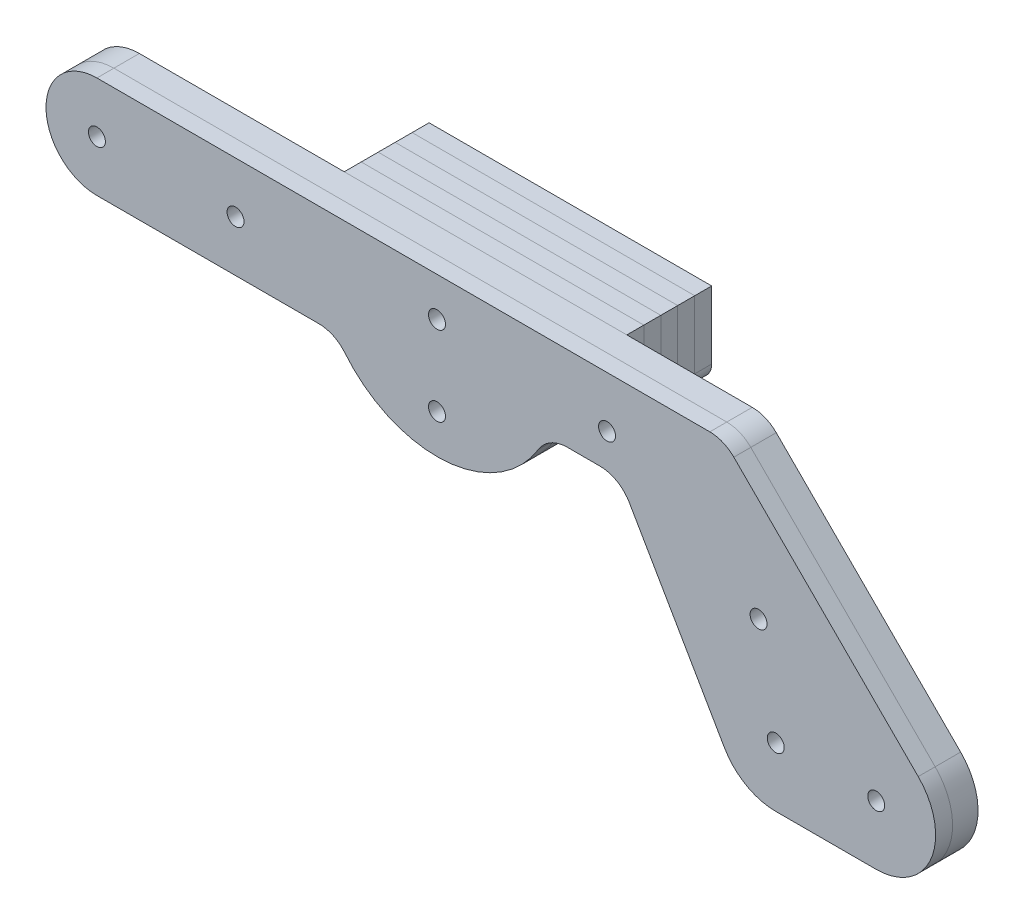
SolidWorks part; units mm, degrees
ref_plane "Plan de face" through (0, 0, 0) normal (0, 0, 1) x (1, 0, 0)
ref_plane "Plan de dessus" through (0, 0, 0) normal (0, 1, 0) x (1, 0, 0)
ref_plane "Plan de droite" through (0, 0, 0) normal (1, 0, 0) x (0, 0, -1)
sketch "Sketch1" plane through (0, 0, 0) normal (0, 0, 1) x (1, 0, 0)
  circle A2 centre (254, 88.9) radius 3.175
  circle A3 centre (127.2504, 56.684) radius 61.5791
  arc A5 (11.6608, 3.5596) -> (11.9167, 2.5763) centre (0, 0) ccw
  circle A7 centre (291.5916, -30.7687) radius 3.175
sketch "Sketch2" plane through (0, 0, 0) normal (0, 0, 1) x (1, 0, 0)
  line L0 (0, 177.334) -> (234.5886, 177.334)
  line L2 (0, 139.234) -> (89.5074, 139.234)
  line L3 (195.5599, 145.6713) -> (234.7526, 77.7875)
  line L4 (168.3037, 145.6713) -> (195.5599, 145.6713)
  line L5 (254, 66.675) -> (291.5916, 66.675)
  line L6 (234.5886, 177.334) -> (307.3071, 104.6154)
  arc A0 (89.5074, 139.234) -> (168.3037, 145.6713) centre (127.2504, 162.7131) ccw
  circle A1 centre (254, 88.9) radius 6.35
  arc A2 (234.7526, 77.7875) -> (254, 66.675) centre (254, 88.9) ccw
  arc A3 (0, 177.334) -> (0, 139.234) centre (0, 158.284) ccw
  circle A4 centre (127.2504, 56.684) radius 61.5791 construction
  circle A5 centre (0, 158.284) radius 6.35
  arc A6 (291.5916, 66.675) -> (307.3071, 104.6154) centre (291.5916, 88.9) ccw
  circle A7 centre (291.5916, 88.9) radius 6.35
  circle A8 centre (51.8605, 158.284) radius 6.35
  circle A9 centre (127.2504, 162.7131) radius 6.35
  circle A10 centre (190.8637, 158.284) radius 6.35
  circle A11 centre (247.5726, 125.7558) radius 6.35
  circle A12 centre (127.2504, 132.884) radius 6.35
  dimension "D1" = 12.7
  dimension "D2" = 88.9
  dimension "D3" = 44.45
  dimension "D7" = 19.05
  dimension "D4" = 45
  dimension "D5" = 60
  dimension "D6" = 101.6
  dimension "D8" = 76.2
extrude "Boss-Extrude1" add sketch "Sketch2" along normal blind 9.525
fillet "Fillet1" radius 12.7 4 edges at (89.5074, 139.234, 4.7625) (168.3037, 145.6713, 4.7625) (195.5599, 145.6713, 4.7625) (234.5886, 177.334, 4.7625)
sketch "Sketch3" plane through (0, 0, 9.525) normal (0, 0, 1) x (1, 0, 0)
  line L5 (0, 139.234) -> (83.0102, 139.234)
  line L6 (176.0515, 145.6713) -> (188.2275, 145.6713)
  line L7 (199.2261, 139.3213) -> (234.7526, 77.7875)
  line L8 (307.3071, 104.6154) -> (238.3083, 173.6143)
  line L9 (229.328, 177.334) -> (0, 177.334)
  line L10 (0, 139.234) -> (83.0102, 139.234)
  line L11 (176.0515, 145.6713) -> (188.2275, 145.6713)
  line L12 (199.2261, 139.3213) -> (234.7526, 77.7875)
  line L14 (229.328, 177.334) -> (0, 177.334)
  line L16 (307.3071, 104.6154) -> (238.3083, 173.6143)
  line L17 (254, 66.675) -> (291.5916, 66.675)
  line L18 (254, 66.675) -> (291.5916, 66.675)
  circle A0 centre (0, 158.284) radius 3.175
  circle A1 centre (254, 88.9) radius 3.175
  circle A2 centre (291.5916, 88.9) radius 3.175
  arc A3 (0, 177.334) -> (0, 139.234) centre (0, 158.284) ccw
  arc A4 (92.8413, 134.5738) -> (165.2068, 139.5806) centre (127.2504, 162.7131) ccw
  arc A5 (234.7526, 77.7875) -> (254, 66.675) centre (254, 88.9) ccw
  arc A6 (0, 177.334) -> (0, 139.234) centre (0, 158.284) ccw
  arc A7 (92.8413, 134.5738) -> (165.2068, 139.5806) centre (127.2504, 162.7131) ccw
  arc A8 (234.7526, 77.7875) -> (254, 66.675) centre (254, 88.9) ccw
  circle A9 centre (51.8605, 158.284) radius 3.175
  circle A10 centre (127.2504, 162.7131) radius 3.175
  circle A11 centre (190.8637, 158.284) radius 3.175
  circle A12 centre (247.5726, 125.7558) radius 3.175
  circle A13 centre (127.2504, 132.884) radius 3.175
  circle A14 centre (127.2504, 132.884) radius 6.35 construction
  arc A24 (291.5916, 66.675) -> (307.3071, 104.6154) centre (291.5916, 88.9) ccw
  arc A25 (291.5916, 66.675) -> (307.3071, 104.6154) centre (291.5916, 88.9) ccw
  arc A29 (238.3083, 173.6143) -> (229.328, 177.334) centre (229.328, 164.634) ccw
  arc A30 (238.3083, 173.6143) -> (229.328, 177.334) centre (229.328, 164.634) ccw
  arc A31 (92.8413, 134.5738) -> (83.0102, 139.234) centre (83.0102, 126.534) ccw
  arc A32 (92.8413, 134.5738) -> (83.0102, 139.234) centre (83.0102, 126.534) ccw
  arc A33 (176.0515, 145.6713) -> (165.2068, 139.5806) centre (176.0515, 132.9713) ccw
  arc A34 (176.0515, 145.6713) -> (165.2068, 139.5806) centre (176.0515, 132.9713) ccw
  arc A35 (199.2261, 139.3213) -> (188.2275, 145.6713) centre (188.2275, 132.9713) ccw
  arc A36 (199.2261, 139.3213) -> (188.2275, 145.6713) centre (188.2275, 132.9713) ccw
  dimension "D2" = 6.35
  dimension "D1" = 0
extrude "Boss-Extrude2" add sketch "Sketch3" along normal blind 6.35 separate body
sketch "Sketch4" [suppressed] plane through (0, 0, 0) normal (0, 0, -1) x (-1, 0, 0)
  line L5 (-238.3083, 173.6143) -> (-307.3071, 104.6154)
  line L6 (-234.7526, 77.7875) -> (-199.2261, 139.3213)
  line L7 (-188.2275, 145.6713) -> (-176.0515, 145.6713)
  line L8 (-83.0102, 139.234) -> (0, 139.234)
  line L9 (0, 177.334) -> (-229.328, 177.334)
  line L11 (-234.7526, 77.7875) -> (-199.2261, 139.3213)
  line L12 (-188.2275, 145.6713) -> (-176.0515, 145.6713)
  line L13 (-83.0102, 139.234) -> (0, 139.234)
  line L14 (0, 177.334) -> (-229.328, 177.334)
  line L16 (-238.3083, 173.6143) -> (-307.3071, 104.6154)
  line L17 (-291.5916, 66.675) -> (-254, 66.675)
  line L18 (-291.5916, 66.675) -> (-254, 66.675)
  circle A0 centre (-291.5916, 88.9) radius 3.175
  circle A1 centre (-254, 88.9) radius 3.175
  circle A2 centre (-254, 88.9) radius 3.175
  circle A3 centre (0, 158.284) radius 3.175
  circle A4 centre (0, 158.284) radius 3.175
  circle A5 centre (-247.5726, 125.7558) radius 3.175
  circle A6 centre (-190.8637, 158.284) radius 3.175
  arc A7 (-254, 66.675) -> (-234.7526, 77.7875) centre (-254, 88.9) ccw
  arc A8 (-165.2068, 139.5806) -> (-92.8413, 134.5738) centre (-127.2504, 162.7131) ccw
  arc A9 (0, 139.234) -> (0, 177.334) centre (0, 158.284) ccw
  arc A10 (-254, 66.675) -> (-234.7526, 77.7875) centre (-254, 88.9) ccw
  arc A11 (-165.2068, 139.5806) -> (-92.8413, 134.5738) centre (-127.2504, 162.7131) ccw
  arc A12 (0, 139.234) -> (0, 177.334) centre (0, 158.284) ccw
  circle A13 centre (-127.2504, 162.7131) radius 3.175
  arc A14 (-307.3071, 104.6154) -> (-291.5916, 66.675) centre (-291.5916, 88.9) ccw
  arc A15 (-307.3071, 104.6154) -> (-291.5916, 66.675) centre (-291.5916, 88.9) ccw
  circle A16 centre (-51.8605, 158.284) radius 3.175
  circle A17 centre (-127.2504, 132.884) radius 3.175
  circle A18 centre (-127.2504, 132.884) radius 6.35 construction
  arc A27 (-188.2275, 145.6713) -> (-199.2261, 139.3213) centre (-188.2275, 132.9713) ccw
  arc A28 (-188.2275, 145.6713) -> (-199.2261, 139.3213) centre (-188.2275, 132.9713) ccw
  arc A29 (-165.2068, 139.5806) -> (-176.0515, 145.6713) centre (-176.0515, 132.9713) ccw
  arc A30 (-165.2068, 139.5806) -> (-176.0515, 145.6713) centre (-176.0515, 132.9713) ccw
  arc A31 (-83.0102, 139.234) -> (-92.8413, 134.5738) centre (-83.0102, 126.534) ccw
  arc A32 (-83.0102, 139.234) -> (-92.8413, 134.5738) centre (-83.0102, 126.534) ccw
  arc A33 (-229.328, 177.334) -> (-238.3083, 173.6143) centre (-229.328, 164.634) ccw
  arc A34 (-229.328, 177.334) -> (-238.3083, 173.6143) centre (-229.328, 164.634) ccw
  dimension "D1" = 0
  dimension "D2" = 0
  dimension "D3" = 0
extrude "Boss-Extrude3" [suppressed] add sketch "Sketch4" along normal blind 6.35 separate body
delete or keep bodies "Body-Delete/Keep 1" [suppressed] type delete bodies bodies 102
sketch "Sketch5" plane through (0, 0, 0) normal (0, 0, -1) x (-1, 0, 0)
  line L0 (-182.4015, 152.0213) -> (-182.4015, 177.334)
  line L1 (-229.328, 177.334) -> (0, 177.334) construction
  line L3 (-76.6602, 145.584) -> (-76.6602, 177.334)
  line L4 (-76.6602, 177.334) -> (-182.4015, 177.334)
  arc A0 (-83.0102, 139.234) -> (-92.8413, 134.5738) centre (-83.0102, 126.534) ccw construction
  arc A1 (-165.2068, 139.5806) -> (-176.0515, 145.6713) centre (-176.0515, 132.9713) ccw construction
  arc A2 (-165.2068, 139.5806) -> (-92.8413, 134.5738) centre (-127.2504, 162.7131) ccw construction
  arc A3 (-83.0102, 139.234) -> (-92.8413, 134.5738) centre (-83.0102, 126.534) ccw
  arc A4 (-165.2068, 139.5806) -> (-176.0515, 145.6713) centre (-176.0515, 132.9713) ccw
  arc A5 (-165.2068, 139.5806) -> (-92.8413, 134.5738) centre (-127.2504, 162.7131) ccw
  arc A6 (-182.4015, 152.0213) -> (-176.0515, 145.6713) centre (-176.0515, 152.0213) ccw
  arc A7 (-83.0102, 139.234) -> (-76.6602, 145.584) centre (-83.0102, 145.584) ccw
  circle A8 centre (-127.2504, 162.7131) radius 6.35 construction
  circle A9 centre (-127.2504, 162.7131) radius 6.35
  circle A10 centre (-127.2504, 132.884) radius 6.35 construction
  circle A11 centre (-127.2504, 132.884) radius 6.35
  dimension "D1" = 12.7
extrude "Boss-Extrude4" add sketch "Sketch5" along normal blind 6.35 separate body
pattern_linear "LPattern1" count 5 spacing 6.35 along (0, 0, -1) of bodies 104
sketch "Sketch6" [suppressed] plane through (0, 0, 9.525) normal (0, 0, 1) x (1, 0, 0)
  line L3 (76.6602, 177.334) -> (76.6602, 145.584)
  line L4 (182.4015, 177.334) -> (76.6602, 177.334)
  line L5 (182.4015, 152.0213) -> (182.4015, 177.334)
  line L6 (76.6602, 177.334) -> (76.6602, 145.584)
  line L7 (182.4015, 177.334) -> (76.6602, 177.334)
  line L8 (182.4015, 152.0213) -> (182.4015, 177.334)
  circle A1 centre (127.2504, 132.884) radius 6.35
  circle A2 centre (127.2504, 132.884) radius 6.35
  circle A3 centre (127.2504, 162.7131) radius 6.35
  circle A4 centre (127.2504, 162.7131) radius 6.35
  arc A9 (176.0515, 145.6713) -> (182.4015, 152.0213) centre (176.0515, 152.0213) ccw
  arc A10 (176.0515, 145.6713) -> (165.2068, 139.5806) centre (176.0515, 132.9713) ccw
  arc A11 (92.8413, 134.5738) -> (165.2068, 139.5806) centre (127.2504, 162.7131) ccw
  arc A12 (92.8413, 134.5738) -> (83.0102, 139.234) centre (83.0102, 126.534) ccw
  arc A13 (76.6602, 145.584) -> (83.0102, 139.234) centre (83.0102, 145.584) ccw
  arc A14 (176.0515, 145.6713) -> (182.4015, 152.0213) centre (176.0515, 152.0213) ccw
  arc A15 (176.0515, 145.6713) -> (165.2068, 139.5806) centre (176.0515, 132.9713) ccw
  arc A16 (92.8413, 134.5738) -> (165.2068, 139.5806) centre (127.2504, 162.7131) ccw
  arc A17 (92.8413, 134.5738) -> (83.0102, 139.234) centre (83.0102, 126.534) ccw
  arc A18 (76.6602, 145.584) -> (83.0102, 139.234) centre (83.0102, 145.584) ccw
  dimension "D1" = 0
  dimension "D2" = 0
  dimension "D3" = 0
extrude "Boss-Extrude5" [suppressed] add sketch "Sketch6" along normal blind 6.35 separate body
pattern_linear "LPattern2" [suppressed] count 5 spacing 6.35
equation "\"Cout/Uni\"= ( ( \"Coût Achat\" + \"Coût Modif\" ) / \"Nb/Paquet\" )"
